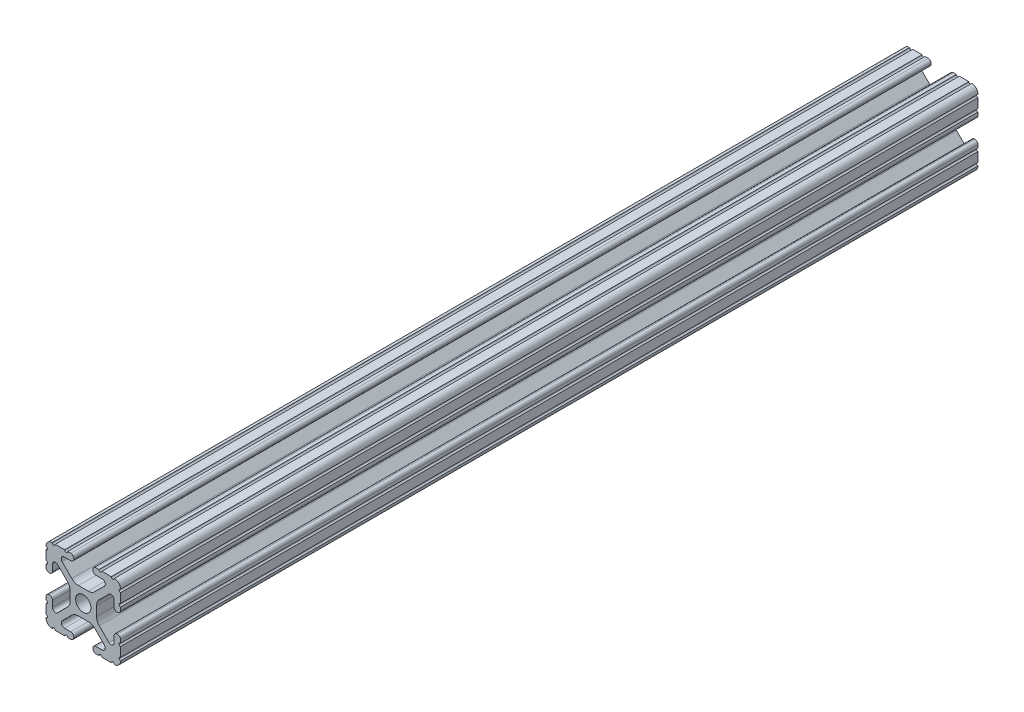
SolidWorks part; units mm, degrees
ref_plane "Front Plane" through (0, 0, 0) normal (0, 0, 1) x (1, 0, 0)
ref_plane "Top Plane" through (0, 0, 0) normal (0, 1, 0) x (1, 0, 0)
ref_plane "Right Plane" through (0, 0, 0) normal (1, 0, 0) x (0, 0, -1)
sketch "Sketch1" plane through (0, 0, 0) normal (0, 0, 1) x (1, 0, 0)
  line L88 (-7.1797, -8.6452) -> (-3.9523, -5.4237)
  line L89 (-1.7093, -4.4958) -> (1.7093, -4.4958)
  line L90 (3.9523, -5.4237) -> (7.1797, -8.6452)
  line L91 (6.4164, -10.4902) -> (4.2875, -10.4902)
  line L92 (3.2385, -11.5392) -> (3.2385, -11.651)
  line L93 (4.2875, -12.7) -> (5.3171, -12.7)
  line L94 (6.3331, -12.7) -> (9.5504, -12.7)
  line L95 (12.7, -9.5504) -> (12.7, -6.3331)
  line L96 (12.7, -5.3171) -> (12.7, -4.2875)
  line L97 (11.651, -3.2385) -> (11.5392, -3.2385)
  line L98 (10.4902, -4.2875) -> (10.4902, -6.4021)
  line L99 (8.7371, -7.1294) -> (5.441, -3.8408)
  line L100 (4.5085, -1.5932) -> (4.5085, 1.5932)
  line L101 (5.441, 3.8408) -> (8.7371, 7.1294)
  line L102 (10.4902, 6.4021) -> (10.4902, 4.2875)
  line L103 (11.5392, 3.2385) -> (11.651, 3.2385)
  line L104 (12.7, 4.2875) -> (12.7, 5.3171)
  line L105 (12.7, 6.3331) -> (12.7, 9.5504)
  line L106 (9.5504, 12.7) -> (6.3331, 12.7)
  line L107 (5.3171, 12.7) -> (4.2875, 12.7)
  line L108 (3.2385, 11.651) -> (3.2385, 11.5392)
  line L109 (4.2875, 10.4902) -> (6.4768, 10.4902)
  line L110 (7.207, 8.7244) -> (3.8983, 5.4232)
  line L111 (1.6558, 4.4958) -> (-1.6558, 4.4958)
  line L112 (-3.8983, 5.4232) -> (-7.207, 8.7244)
  line L113 (-6.4768, 10.4902) -> (-4.2875, 10.4902)
  line L114 (-3.2385, 11.5392) -> (-3.2385, 11.651)
  line L115 (-4.2875, 12.7) -> (-5.3171, 12.7)
  line L116 (-6.3331, 12.7) -> (-9.5504, 12.7)
  line L117 (-12.7, 9.5504) -> (-12.7, 6.3331)
  line L118 (-12.7, 5.3171) -> (-12.7, 4.2875)
  line L119 (-11.651, 3.2385) -> (-11.5392, 3.2385)
  line L120 (-10.4902, 4.2875) -> (-10.4902, 6.4021)
  line L121 (-8.7371, 7.1294) -> (-5.441, 3.8408)
  line L122 (-4.5085, 1.5932) -> (-4.5085, -1.5932)
  line L123 (-5.441, -3.8408) -> (-8.7371, -7.1294)
  line L124 (-10.4902, -6.4021) -> (-10.4902, -4.2875)
  line L125 (-11.5392, -3.2385) -> (-11.651, -3.2385)
  line L126 (-12.7, -4.2875) -> (-12.7, -5.3171)
  line L127 (-12.7, -6.3331) -> (-12.7, -9.5504)
  line L128 (-9.5504, -12.7) -> (-6.3331, -12.7)
  line L129 (-5.3171, -12.7) -> (-4.2875, -12.7)
  line L130 (-3.2385, -11.651) -> (-3.2385, -11.5392)
  line L131 (-4.2875, -10.4902) -> (-6.4164, -10.4902)
  circle A1 centre (0, 0) radius 2.6035
  arc A104 (-7.1797, -8.6452) -> (-6.4164, -10.4902) centre (-6.4164, -9.4098) ccw
  arc A105 (-1.7093, -4.4958) -> (-3.9523, -5.4237) centre (-1.7093, -7.6708) ccw
  arc A106 (3.9523, -5.4237) -> (1.7093, -4.4958) centre (1.7093, -7.6708) ccw
  arc A107 (6.4164, -10.4902) -> (7.1797, -8.6452) centre (6.4164, -9.4098) ccw
  arc A108 (4.2875, -10.4902) -> (3.2385, -11.5392) centre (4.2875, -11.5392) ccw
  arc A109 (3.2385, -11.651) -> (4.2875, -12.7) centre (4.2875, -11.651) ccw
  arc A110 (6.3331, -12.7) -> (5.3171, -12.7) centre (5.8251, -12.7) ccw
  arc A111 (10.5664, -12.6998) -> (9.5504, -12.7) centre (10.0584, -12.7) ccw
  arc A112 (10.5664, -12.6998) -> (12.6998, -10.5664) centre (10.5918, -10.5918) ccw
  arc A113 (12.7, -9.5504) -> (12.6998, -10.5664) centre (12.7, -10.0584) ccw
  arc A114 (12.7, -5.3171) -> (12.7, -6.3331) centre (12.7, -5.8251) ccw
  arc A115 (12.7, -4.2875) -> (11.651, -3.2385) centre (11.651, -4.2875) ccw
  arc A116 (11.5392, -3.2385) -> (10.4902, -4.2875) centre (11.5392, -4.2875) ccw
  arc A117 (8.7371, -7.1294) -> (10.4902, -6.4021) centre (9.4628, -6.4021) ccw
  arc A118 (4.5085, -1.5932) -> (5.441, -3.8408) centre (7.6835, -1.5932) ccw
  arc A119 (5.441, 3.8408) -> (4.5085, 1.5932) centre (7.6835, 1.5932) ccw
  arc A120 (10.4902, 6.4021) -> (8.7371, 7.1294) centre (9.4628, 6.4021) ccw
  arc A121 (10.4902, 4.2875) -> (11.5392, 3.2385) centre (11.5392, 4.2875) ccw
  arc A122 (11.651, 3.2385) -> (12.7, 4.2875) centre (11.651, 4.2875) ccw
  arc A123 (12.7, 6.3331) -> (12.7, 5.3171) centre (12.7, 5.8251) ccw
  arc A124 (12.6998, 10.5664) -> (12.7, 9.5504) centre (12.7, 10.0584) ccw
  arc A125 (12.6998, 10.5664) -> (10.5664, 12.6998) centre (10.5918, 10.5918) ccw
  arc A126 (9.5504, 12.7) -> (10.5664, 12.6998) centre (10.0584, 12.7) ccw
  arc A127 (5.3171, 12.7) -> (6.3331, 12.7) centre (5.8251, 12.7) ccw
  arc A128 (4.2875, 12.7) -> (3.2385, 11.651) centre (4.2875, 11.651) ccw
  arc A129 (3.2385, 11.5392) -> (4.2875, 10.4902) centre (4.2875, 11.5392) ccw
  arc A130 (7.207, 8.7244) -> (6.4768, 10.4902) centre (6.4768, 9.4563) ccw
  arc A131 (1.6558, 4.4958) -> (3.8983, 5.4232) centre (1.6558, 7.6708) ccw
  arc A132 (-3.8983, 5.4232) -> (-1.6558, 4.4958) centre (-1.6558, 7.6708) ccw
  arc A133 (-6.4768, 10.4902) -> (-7.207, 8.7244) centre (-6.4768, 9.4563) ccw
  arc A134 (-4.2875, 10.4902) -> (-3.2385, 11.5392) centre (-4.2875, 11.5392) ccw
  arc A135 (-3.2385, 11.651) -> (-4.2875, 12.7) centre (-4.2875, 11.651) ccw
  arc A136 (-6.3331, 12.7) -> (-5.3171, 12.7) centre (-5.8251, 12.7) ccw
  arc A137 (-10.5664, 12.6998) -> (-9.5504, 12.7) centre (-10.0584, 12.7) ccw
  arc A138 (-10.5664, 12.6998) -> (-12.6998, 10.5664) centre (-10.5918, 10.5918) ccw
  arc A139 (-12.7, 9.5504) -> (-12.6998, 10.5664) centre (-12.7, 10.0584) ccw
  arc A140 (-12.7, 5.3171) -> (-12.7, 6.3331) centre (-12.7, 5.8251) ccw
  arc A141 (-12.7, 4.2875) -> (-11.651, 3.2385) centre (-11.651, 4.2875) ccw
  arc A142 (-11.5392, 3.2385) -> (-10.4902, 4.2875) centre (-11.5392, 4.2875) ccw
  arc A143 (-8.7371, 7.1294) -> (-10.4902, 6.4021) centre (-9.4628, 6.4021) ccw
  arc A144 (-4.5085, 1.5932) -> (-5.441, 3.8408) centre (-7.6835, 1.5932) ccw
  arc A145 (-5.441, -3.8408) -> (-4.5085, -1.5932) centre (-7.6835, -1.5932) ccw
  arc A146 (-10.4902, -6.4021) -> (-8.7371, -7.1294) centre (-9.4628, -6.4021) ccw
  arc A147 (-10.4902, -4.2875) -> (-11.5392, -3.2385) centre (-11.5392, -4.2875) ccw
  arc A148 (-11.651, -3.2385) -> (-12.7, -4.2875) centre (-11.651, -4.2875) ccw
  arc A149 (-12.7, -6.3331) -> (-12.7, -5.3171) centre (-12.7, -5.8251) ccw
  arc A150 (-12.6998, -10.5664) -> (-12.7, -9.5504) centre (-12.7, -10.0584) ccw
  arc A151 (-12.6998, -10.5664) -> (-10.5664, -12.6998) centre (-10.5918, -10.5918) ccw
  arc A152 (-9.5504, -12.7) -> (-10.5664, -12.6998) centre (-10.0584, -12.7) ccw
  arc A153 (-5.3171, -12.7) -> (-6.3331, -12.7) centre (-5.8251, -12.7) ccw
  arc A154 (-4.2875, -12.7) -> (-3.2385, -11.651) centre (-4.2875, -11.651) ccw
  arc A155 (-3.2385, -11.5392) -> (-4.2875, -10.4902) centre (-4.2875, -11.5392) ccw
extrude "Boss-Extrude1" add sketch "Sketch1" along normal mid plane 292.1
